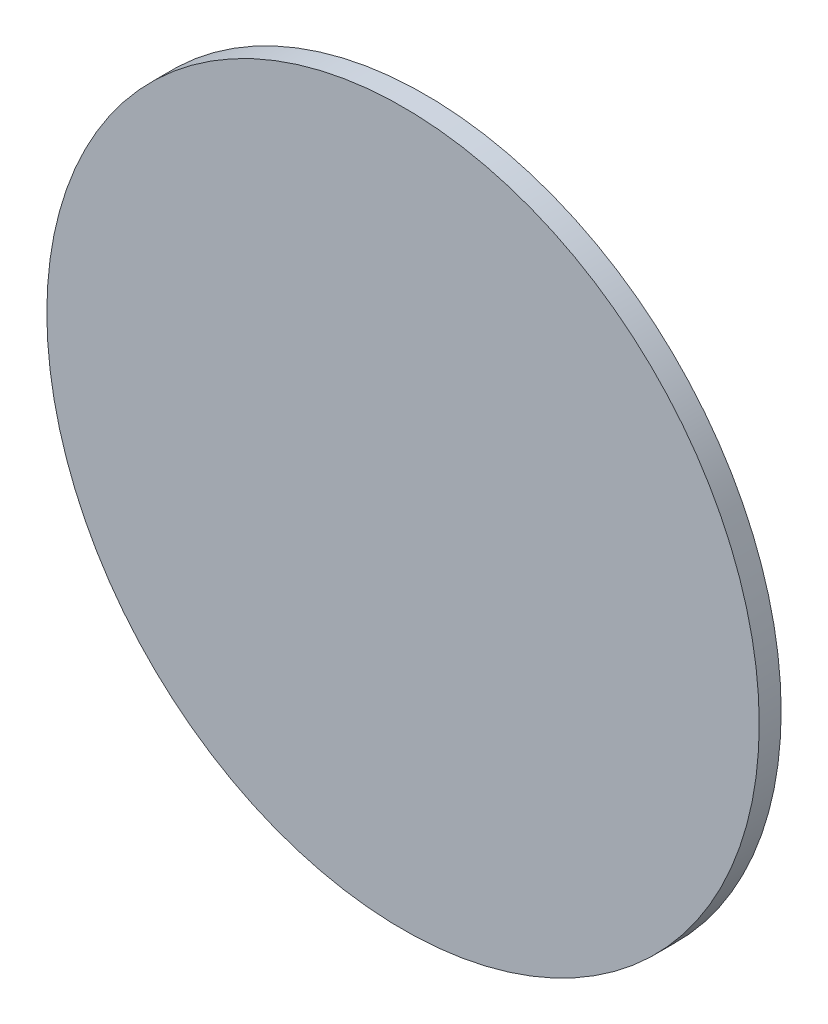
SolidWorks part; units mm, degrees
ref_plane "Front Plane" through (0, 0, 0) normal (0, 0, 1) x (1, 0, 0)
ref_plane "Top Plane" through (0, 0, 0) normal (0, 1, 0) x (1, 0, 0)
ref_plane "Right Plane" through (0, 0, 0) normal (1, 0, 0) x (0, 0, -1)
sketch "Sketch1" plane through (0, 0, 0) normal (0, 0, 1) x (1, 0, 0)
  circle A0 centre (0, 0) radius 13
  dimension "D1" = 26
extrude "Boss-Extrude1" add sketch "Sketch1" along normal blind 0.8
